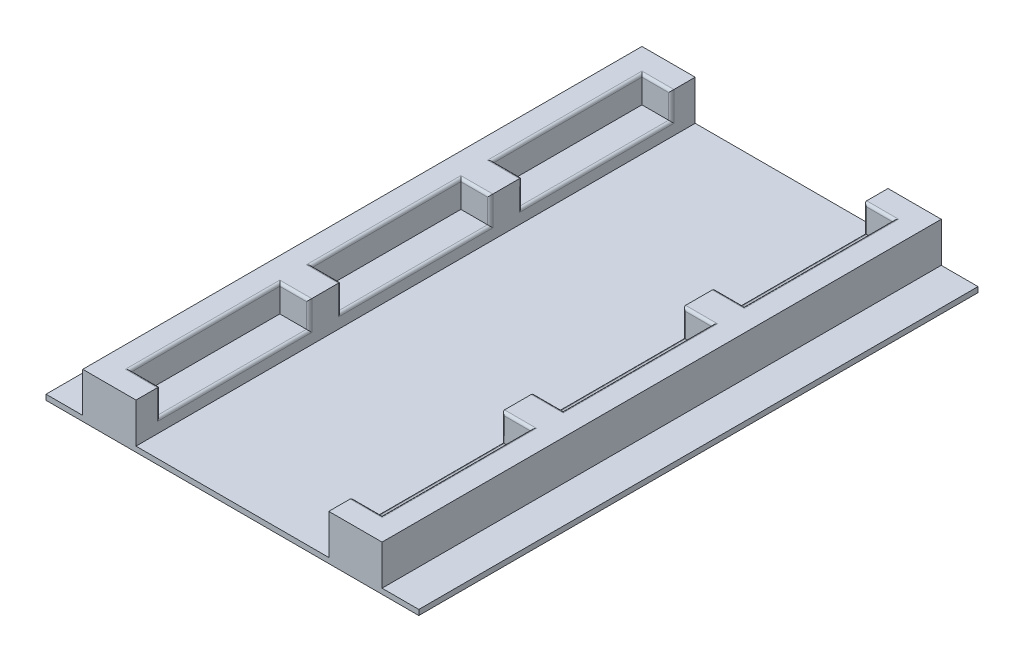
SolidWorks part; units mm, degrees
ref_plane "Ebene vorne" through (0, 0, 0) normal (0, 0, 1) x (1, 0, 0)
ref_plane "Ebene oben" through (0, 0, 0) normal (0, 1, 0) x (1, 0, 0)
ref_plane "Ebene rechts" through (0, 0, 0) normal (1, 0, 0) x (0, 0, -1)
sketch "Skizze1" plane through (0, 0, 0) normal (0, 1, 0) x (1, 0, 0)
  line L1 (-70, -105) -> (70, -105)
  line L2 (-70, -105) -> (-70, 105)
  line L3 (-70, 105) -> (70, 105)
  line L4 (70, -105) -> (70, 105)
  line L5 (-70, -105) -> (70, 105) construction
  line L6 (-70, 105) -> (70, -105) construction
  point P0 (0, 0)
  dimension "D1" = 210
  dimension "D2" = 140
extrude "Aufsatz-Linear austragen1" add sketch "Skizze1" along normal blind 2
sketch "Skizze2" plane through (0, 2, 0) normal (0, 1, 0) x (1, 0, 0)
  line L0 (0, 105) -> (0, -105) construction
  line L1 (-46.2, -27) -> (46.2, -27) construction
  line L2 (-46.2, -27) -> (-46.2, 27) construction
  line L3 (-46.2, 27) -> (46.2, 27) construction
  line L4 (46.2, -27) -> (46.2, 27) construction
  line L5 (-46.2, -27) -> (46.2, 27) construction
  line L6 (-46.2, 27) -> (46.2, -27) construction
  line L7 (70, 105) -> (-70, 105) construction
  line L8 (-70, -105) -> (70, -105) construction
  line L9 (-45.4738, -92.1512) -> (45.4738, -92.1512) construction
  line L10 (-46.2, 39) -> (46.2, 39) construction
  line L11 (-46.2, 39) -> (-46.2, 93) construction
  line L12 (-46.2, 93) -> (46.2, 93) construction
  line L13 (46.2, 39) -> (46.2, 93) construction
  line L14 (-46.2, 39) -> (46.2, 93) construction
  line L15 (-46.2, 93) -> (46.2, 39) construction
  line L16 (-45.4738, -92.1512) -> (-45.4738, -39) construction
  line L17 (-45.4738, -39) -> (45.4738, -39) construction
  line L18 (45.4738, -92.1512) -> (45.4738, -39) construction
  line L19 (-45.4738, -92.1512) -> (45.4738, -39) construction
  line L20 (-45.4738, -39) -> (45.4738, -92.1512) construction
  line L22 (-56.2, -105) -> (-36.2, -105)
  line L23 (-56.2, -105) -> (-56.2, 105)
  line L24 (-56.2, 105) -> (-36.2, 105)
  line L25 (-36.2, -105) -> (-36.2, 105)
  line L26 (-56.2, -105) -> (-36.2, 105) construction
  line L27 (-56.2, 105) -> (-36.2, -105) construction
  line L28 (36.2, -105) -> (56.2, -105)
  line L29 (36.2, -105) -> (36.2, 105)
  line L30 (36.2, 105) -> (56.2, 105)
  line L31 (56.2, -105) -> (56.2, 105)
  line L32 (36.2, -105) -> (56.2, 105) construction
  line L33 (36.2, 105) -> (56.2, -105) construction
  point P0 (0, 0)
  point P12 (0, 66)
  point P17 (0, -65.5756)
  point P19 (-46.2, 0)
  point P27 (46.2, 0)
  dimension "D1" = 54
  dimension "D2" = 92.4
  dimension "D3" = 54
  dimension "D4" = 92.4
  dimension "D5" = 12
  dimension "D6" = 12
  dimension "D7" = 20
extrude "Aufsatz-Linear austragen2" add sketch "Skizze2" along normal blind 15
sketch "Skizze3" plane through (0, 17, 0) normal (0, 1, 0) x (1, 0, 0)
  line L0 (0, 105) -> (0, -105) construction
  line L1 (-47.2, -28) -> (47.2, -28)
  line L2 (-47.2, -28) -> (-47.2, 28)
  line L3 (-47.2, 28) -> (47.2, 28)
  line L4 (47.2, -28) -> (47.2, 28)
  line L5 (-47.2, -28) -> (47.2, 28) construction
  line L6 (-47.2, 28) -> (47.2, -28) construction
  line L7 (36.2, 105) -> (-36.2, 105) construction
  line L8 (-36.2, -105) -> (36.2, -105) construction
  line L9 (-47.2, -96) -> (47.2, -96)
  line L10 (-47.2, 40) -> (47.2, 40)
  line L11 (-47.2, 40) -> (-47.2, 96)
  line L12 (-47.2, 96) -> (47.2, 96)
  line L13 (47.2, 40) -> (47.2, 96)
  line L14 (-47.2, 40) -> (47.2, 96) construction
  line L15 (-47.2, 96) -> (47.2, 40) construction
  line L16 (-47.2, -96) -> (-47.2, -40)
  line L17 (-47.2, -40) -> (47.2, -40)
  line L18 (47.2, -96) -> (47.2, -40)
  line L19 (-47.2, -96) -> (47.2, -40) construction
  line L20 (-47.2, -40) -> (47.2, -96) construction
  point P0 (0, 0)
  point P7 (0, 0)
  point P8 (0, 0)
  point P9 (0, 0)
  point P10 (0, 0)
  point P11 (0, 0)
  point P12 (0, 68)
  point P17 (0, -68)
  point P19 (-7.6704, 66)
  point P23 (0, 105)
  point P26 (0, -105)
  point P29 (42.7841, -90.4582)
  point P30 (-84.7384, -77.4288)
  point P31 (-46.2, 39)
  point P33 (-46.2, 27)
  dimension "D1" = 56
  dimension "D2" = 94.4
  dimension "D5" = 12
  dimension "D6" = 12
extrude "Schnitt-Linear austragen1" cut sketch "Skizze3" against normal blind 10
fillet "Verrundung1" radius 1 36 edges at (36.2, 7, -68) (36.2, 7, 0) (36.2, 7, 68) (36.2, 12, 96) (36.2, 12, 40) (36.2, 12, 28) (36.2, 12, -28) (36.2, 12, -40) (36.2, 12, -96) (41.7, 17, -96) (41.7, 17, -40) (41.7, 17, 28) (41.7, 17, -28) (41.7, 17, 96) (41.7, 17, 40) (47.2, 17, 68) (47.2, 17, 0) (47.2, 17, -68) (-36.2, 7, 0) (-36.2, 7, -68) (-36.2, 7, 68) (-36.2, 12, 96) (-36.2, 12, 40) (-36.2, 12, 28) (-36.2, 12, -28) (-36.2, 12, -40) (-36.2, 12, -96) (-41.7, 17, -96) (-47.2, 17, -68) (-41.7, 17, -40) (-41.7, 17, -28) (-47.2, 17, 0) (-41.7, 17, 28) (-41.7, 17, 96) (-47.2, 17, 68) (-41.7, 17, 40)
